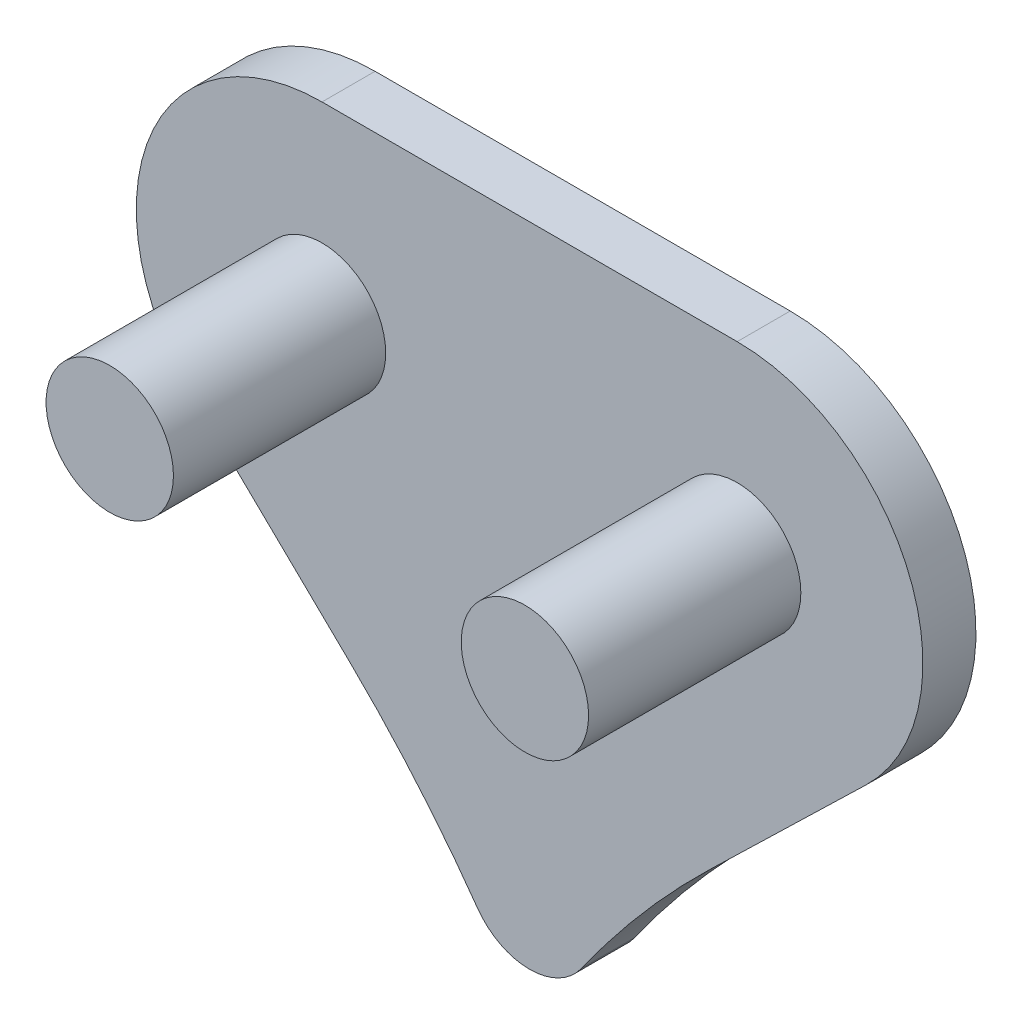
SolidWorks part; units mm, degrees
ref_plane "Front" through (0, 0, 0) normal (0, 0, 1) x (1, 0, 0)
ref_plane "Top" through (0, 0, 0) normal (0, 1, 0) x (1, 0, 0)
ref_plane "Right" through (0, 0, 0) normal (1, 0, 0) x (0, 0, -1)
sketch "Sketch2" plane through (0, 0, 0) normal (0, 0, 1) x (1, 0, 0)
  line L0 (-1.396, 1.75) -> (2.5158, 1.75)
  line L1 (0.5599, 1.75) -> (0.5599, -3.75) construction
  line L2 (-1.1373, -2.6871) -> (-2.6136, -1.2569)
  line L3 (2.2572, -2.6871) -> (3.7335, -1.2569)
  circle A2 centre (-1.396, 0) radius 0.6
  circle A3 centre (2.5158, 0) radius 0.6
  arc A4 (-1.396, 1.75) -> (-2.6136, -1.2569) centre (-1.396, 0) ccw
  arc A5 (3.7335, -1.2569) -> (2.5158, 1.75) centre (2.5158, 0) ccw
  arc A6 (0.07, -4.0964) -> (1.0498, -4.0964) centre (0.5599, -3.75) ccw
  arc A7 (-1.1373, -2.6871) -> (0.07, -4.0964) centre (-8.0952, -9.8695) cw
  arc A8 (2.2572, -2.6871) -> (1.0498, -4.0964) centre (9.2151, -9.8695) ccw
  point P12 (-0.0401, -3.75)
  point P19 (1.1599, -3.75)
  dimension "D2" = 10
  dimension "D3" = 10
  dimension "D1" = 5.5
extrude "Boss-Extrude1" add sketch "Sketch2" along normal blind 0.5
sketch "Sketch3" plane through (0, 0, 0.5) normal (0, 0, 1) x (1, 0, 0)
  circle A0 centre (-1.396, 0) radius 0.6 construction
  circle A1 centre (2.5158, 0) radius 0.6 construction
  circle A2 centre (-1.396, 0) radius 0.6
  circle A3 centre (2.5158, 0) radius 0.6
extrude "Boss-Extrude2" add sketch "Sketch3" along normal blind 2 and the other way blind 0.5
ref_plane "Plane1" through (0, 0, 2.5) normal (0, 0, 1) x (1, 0, 0)
ref_plane "Plane2" through (0, 0, 1.5) normal (0, 0, 1) x (1, 0, 0)
